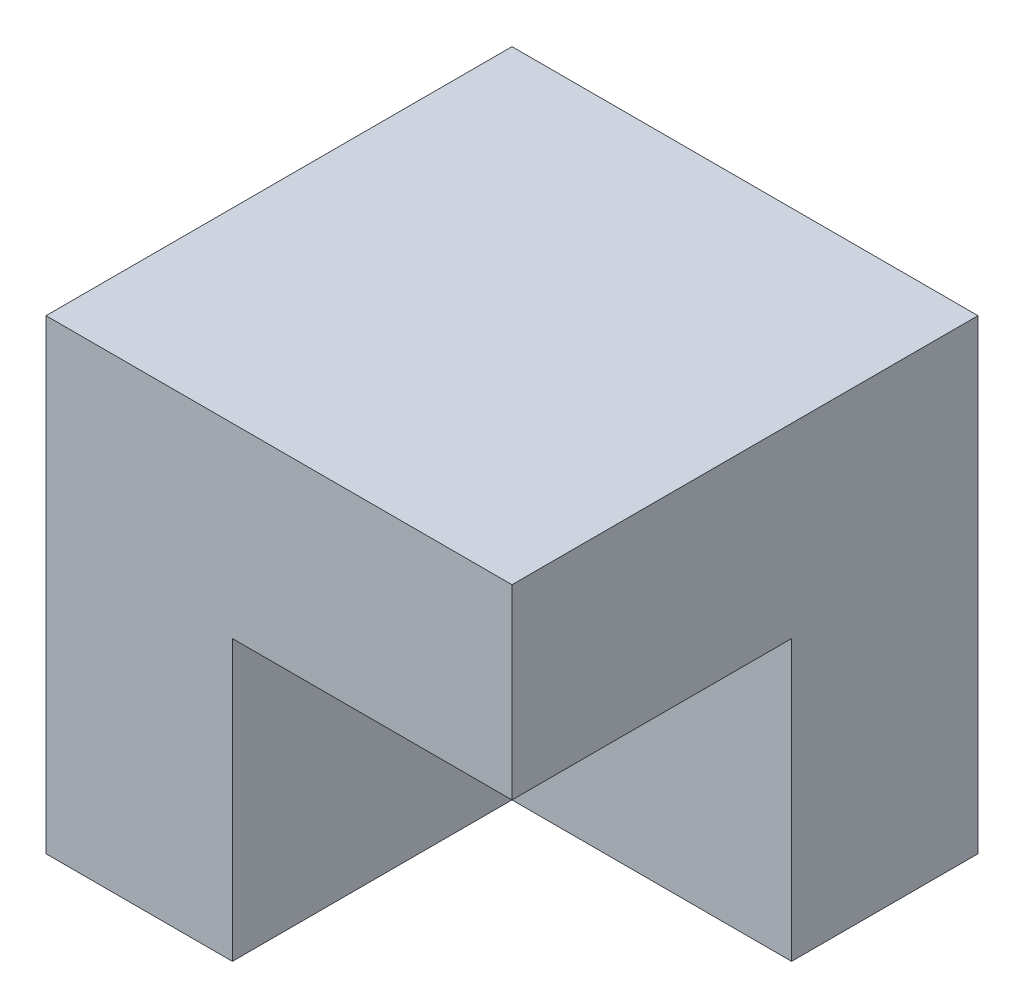
SolidWorks part; units mm, degrees
material "2014-T6"
ref_plane "Front Plane" through (0, 0, 0) normal (0, 0, 1) x (1, 0, 0)
ref_plane "Top Plane" through (0, 0, 0) normal (0, 1, 0) x (1, 0, 0)
ref_plane "Right Plane" through (0, 0, 0) normal (1, 0, 0) x (0, 0, -1)
sketch "Sketch1" plane through (0, 0, 0) normal (0, 1, 0) x (1, 0, 0)
  line L8 (-2.5, 2.5) -> (2.5, 2.5)
  line L9 (-2.5, 2.5) -> (-2.5, -2.5)
  line L10 (-2.5, -2.5) -> (2.5, -2.5)
  line L11 (2.5, 2.5) -> (2.5, -2.5)
  dimension "D1" = 5
  dimension "D2" = 5
  dimension "D3" = 2.5
  dimension "D4" = 2.5
extrude "Boss-Extrude1" add sketch "Sketch1" along normal blind 5
sketch "Sketch2" plane through (0, 0, 0) normal (0, 1, 0) x (1, 0, 0)
  line L0 (2.5, 2.5) -> (-2.5, 2.5) construction
  line L1 (2.5, -2.5) -> (-0.5, -2.5)
  line L2 (2.5, -2.5) -> (2.5, 0.5)
  line L3 (2.5, 0.5) -> (-0.5, 0.5)
  line L4 (-0.5, -2.5) -> (-0.5, 0.5)
  line L5 (-2.5, 2.5) -> (-2.5, -2.5) construction
  dimension "D1" = 2
  dimension "D2" = 2
extrude "Cut-Extrude1" cut sketch "Sketch2" along normal blind 3
